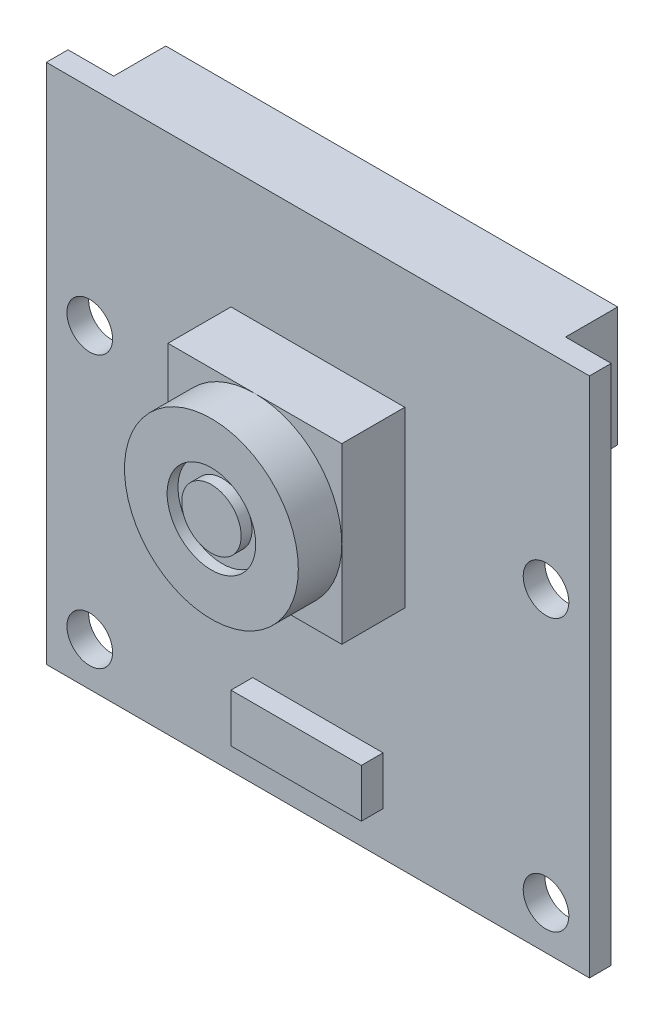
SolidWorks part; units mm, degrees
ref_plane "Front Plane" through (0, 0, 0) normal (0, 0, 1) x (1, 0, 0)
ref_plane "Top Plane" through (0, 0, 0) normal (0, 1, 0) x (1, 0, 0)
ref_plane "Right Plane" through (0, 0, 0) normal (1, 0, 0) x (0, 0, -1)
sketch "Sketch1" plane through (0, 0, 0) normal (0, 0, 1) x (1, 0, 0)
  line L0 (0, 18.1386) -> (0, -22.6892) construction
  line L1 (-12.5, 12) -> (12.5, 12)
  line L2 (-12.5, 12) -> (-12.5, -12)
  line L3 (-12.5, -12) -> (12.5, -12)
  line L4 (12.5, 12) -> (12.5, -12)
  circle A0 centre (-10.5, 2.5) radius 1.05
  circle A1 centre (-10.5, -10) radius 1.05
  circle A2 centre (10.5, -10) radius 1.05
  circle A3 centre (10.5, 2.5) radius 1.05
  point P0 (0, 0)
  dimension "D3" = 2.1
  dimension "D1" = 24
  dimension "D2" = 25
  dimension "D4" = 9.5
  dimension "D5" = 2
  dimension "D6" = 12.5
extrude "Boss-Extrude1" add sketch "Sketch1" along normal blind 1
sketch "Sketch2" plane through (0, 0, 0) normal (0, 0, -1) x (-1, 0, 0)
  line L0 (-12.5, 12) -> (12.5, 12) construction
  line L1 (10.4, 12) -> (-10.4, 12)
  line L2 (10.4, 12) -> (10.4, 6.5)
  line L3 (10.4, 6.5) -> (-10.4, 6.5)
  line L4 (-10.4, 12) -> (-10.4, 6.5)
  line L5 (-12.5, -12) -> (-12.5, 12) construction
  point P8 (-10.4, 9.25)
  dimension "D1" = 5.5
  dimension "D2" = 20.8
  dimension "D3" = 2.1
extrude "Boss-Extrude2" add sketch "Sketch2" along normal blind 2.4
sketch "Sketch3" plane through (0, 0, 1) normal (0, 0, 1) x (1, 0, 0)
  line L0 (12.5, 12) -> (-12.5, 12) construction
  line L1 (-4, -1.5) -> (4, -1.5)
  line L2 (-4, -1.5) -> (-4, 6.5)
  line L3 (-4, 6.5) -> (4, 6.5)
  line L4 (4, -1.5) -> (4, 6.5)
  line L5 (12.5, -12) -> (12.5, 12) construction
  dimension "D1" = 8
  dimension "D2" = 8
  dimension "D3" = 5.5
  dimension "D4" = 8.5
extrude "Boss-Extrude3" add sketch "Sketch3" along normal blind 4.9
sketch "Sketch6" plane through (0, 0, 5.9) normal (0, 0, 1) x (1, 0, 0)
  line L0 (4, 6.5) -> (-4, 6.5) construction
  line L2 (4, -1.5) -> (4, 6.5) construction
  line L4 (-4, -1.5) -> (4, -1.5)
  line L5 (-4, -1.5) -> (-4, 6.5)
  line L6 (-4, 6.5) -> (4, 6.5)
  line L7 (4, -1.5) -> (4, 6.5)
  circle A0 centre (0, 2.5) radius 4
  line M1 (-4, 6.5) -> (-4, -1.5)
  line M2 (-4, -1.5) -> (4, -1.5)
  line M3 (4, -1.5) -> (4, 6.5)
  line M4 (4, 6.5) -> (-4, 6.5)
  dimension "D1" = 8
  dimension "D2" = 4
  dimension "D3" = 4
extrude "Cut-Extrude3" cut sketch "Sketch6" against normal blind 2 contours A0 L6 M1 | A0 L7 M4 | A0 L4 M3 | A0 L5 M2
sketch "Sketch7" plane through (0, 0, 5.9) normal (0, 0, 1) x (1, 0, 0)
  circle A0 centre (0, 2.5) radius 1.3678
  circle A1 centre (0, 2.5) radius 2.0382
extrude "Cut-Extrude4" cut sketch "Sketch7" against normal blind 0.5
sketch "Sketch8" plane through (0, 0, 1) normal (0, 0, 1) x (1, 0, 0)
  line L1 (-3, -10) -> (3, -10)
  line L2 (-3, -10) -> (-3, -7.7754)
  line L3 (-3, -7.7754) -> (3, -7.7754)
  line L4 (3, -10) -> (3, -7.7754)
  dimension "D1" = 6
  dimension "D2" = 1
extrude "Boss-Extrude4" add sketch "Sketch8" along normal blind 1
